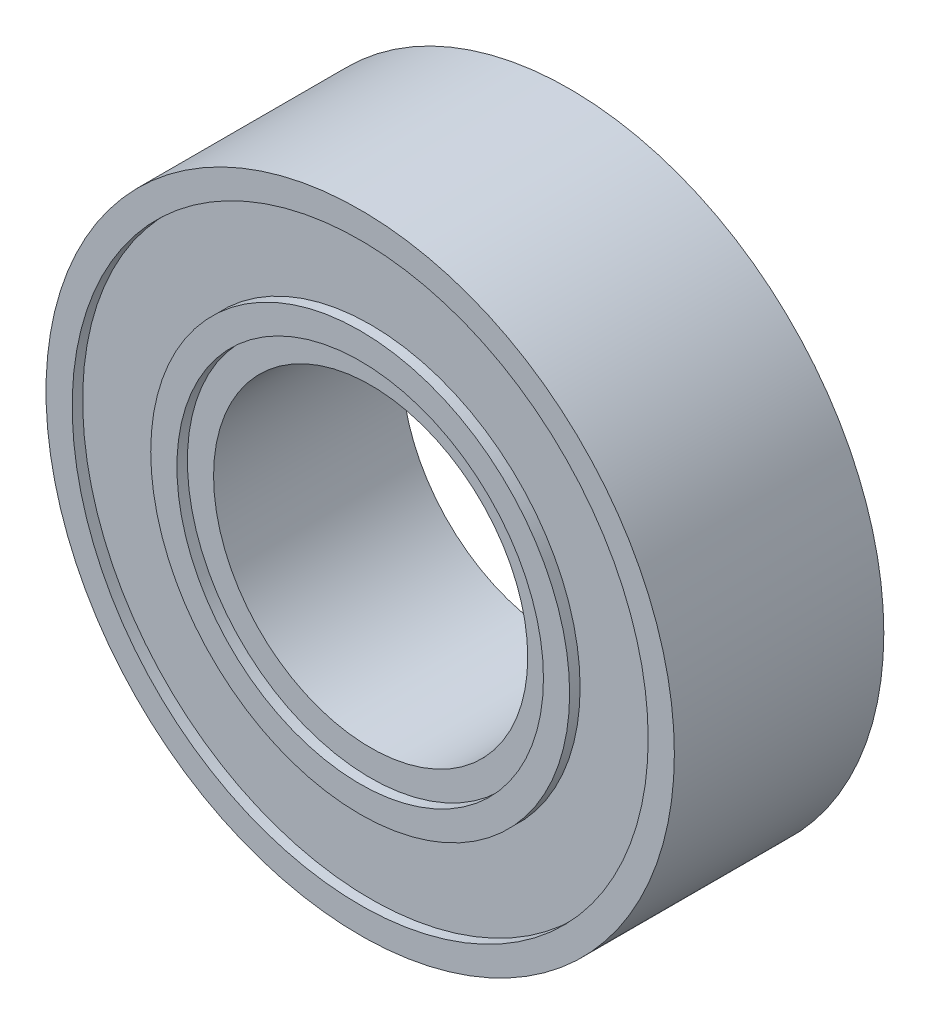
SolidWorks part; units mm, degrees
material "Резина"
ref_plane "Спереди" through (0, 0, 0) normal (0, 0, 1) x (1, 0, 0)
ref_plane "Сверху" through (0, 0, 0) normal (0, 1, 0) x (1, 0, 0)
ref_plane "Справа" through (0, 0, 0) normal (1, 0, 0) x (0, 0, -1)
sketch "Эскиз1" plane through (0, 0, 0) normal (0, 1, 0) x (1, 0, 0)
  line L0 (-3, 0) -> (-6, 0)
  line L1 (-6, 0) -> (-6, 4)
  line L2 (-6, 4) -> (-3, 4)
  line L3 (-3, 4) -> (-3, 0)
  line L4 (0, 0) -> (0, 12544.7981) construction
  dimension "D1" = 3
  dimension "D2" = 6
  dimension "D3" = 4
revolve "Повернуть1" add sketch "Эскиз1" angle 360 about L4
sketch "Эскиз2" plane through (0, 0, 0) normal (0, 0, 1) x (1, 0, 0)
  circle A0 centre (0, 0) radius 3.5
  dimension "D1" = 7
extrude "Вырез-Вытянуть1" cut sketch "Эскиз2" against normal blind 0.2
sketch "Эскиз3" plane through (0, 0, 0) normal (0, 0, 1) x (1, 0, 0)
  circle A0 centre (0, 0) radius 4
  circle A1 centre (0, 0) radius 5.5
  dimension "D1" = 8
  dimension "D2" = 11
extrude "Вырез-Вытянуть2" cut sketch "Эскиз3" against normal blind 0.2
ref_plane "Плоскость1" through (0, 0, -2) normal (0, 0, 1) x (1, 0, 0)
mirror "Зеркальное отражение1" about plane through (0, 0, -2) normal (0, 0, 1) of "Вырез-Вытянуть2", "Вырез-Вытянуть1"
